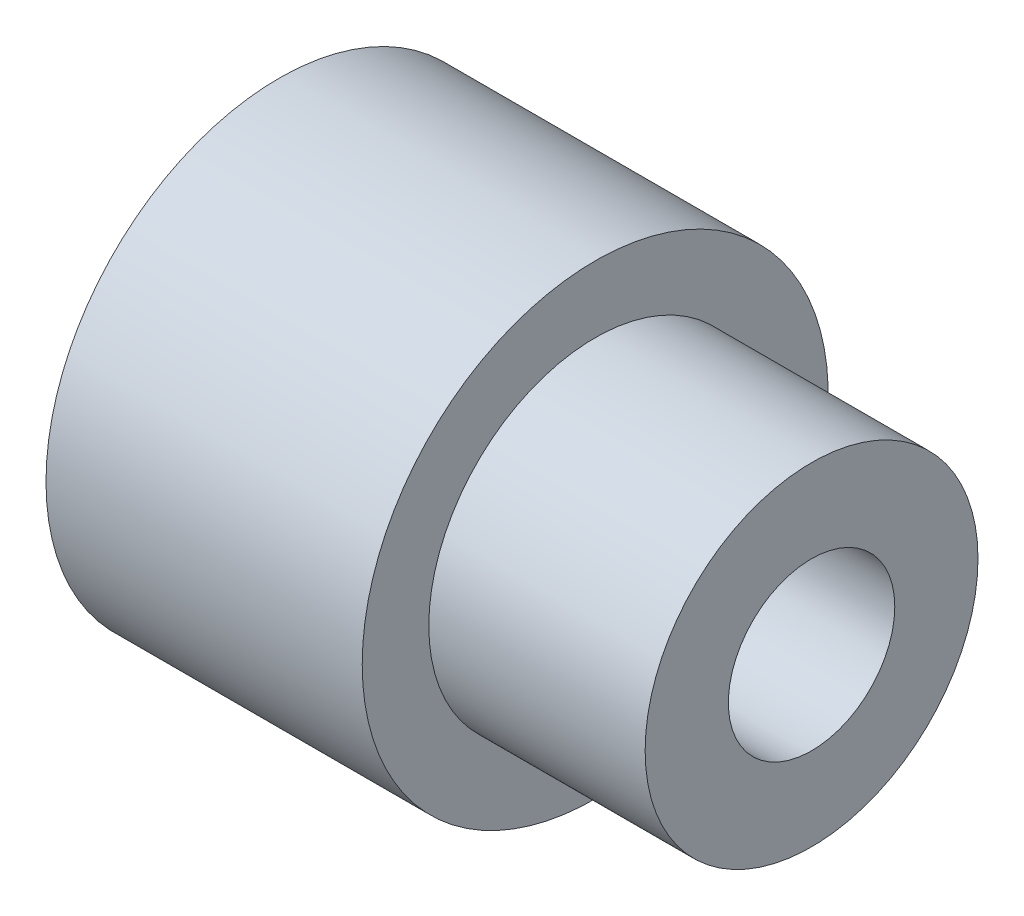
SolidWorks part; units mm, degrees
ref_plane "Front Plane" through (0, 0, 0) normal (0, 0, 1) x (1, 0, 0)
ref_plane "Top Plane" through (0, 0, 0) normal (0, 1, 0) x (1, 0, 0)
ref_plane "Right Plane" through (0, 0, 0) normal (1, 0, 0) x (0, 0, -1)
sketch "Sketch1" plane through (0, 0, 0) normal (0, 0, 1) x (1, 0, 0)
  line L0 (-20.8099, 0) -> (11.1901, 0) construction
  line L1 (-20.8099, 0) -> (-20.8099, -14)
  line L2 (-20.8099, -14) -> (-1.8099, -14)
  line L3 (-1.8099, -14) -> (-1.8099, -10)
  line L4 (-1.8099, -10) -> (11.1901, -10)
  line L5 (11.1901, -10) -> (11.1901, 0)
  line L6 (-20.8099, 0) -> (11.1901, 0)
  dimension "D1" = 14
  dimension "D2" = 19
  dimension "D3" = 13
  dimension "D4" = 4
  dimension "D5" = 10
  dimension "D6" = 32
revolve "Revolve1" add sketch "Sketch1" angle 360 about L0
sketch "Sketch2" plane through (-20.8099, 0, 0) normal (-1, 0, 0) x (0, 0, 1)
  circle A0 centre (0, 0) radius 11
  dimension "D1" = 22
extrude "Cut-Extrude2" cut sketch "Sketch2" against normal blind 6
sketch "Sketch6" plane through (-14.8099, 0, 0) normal (-1, 0, 0) x (0, 0, 1)
  circle A0 centre (0, 0) radius 9
  dimension "D1" = 18
extrude "Cut-Extrude3" cut sketch "Sketch6" against normal blind 10
sketch "Sketch7" plane through (11.1901, 0, 0) normal (1, 0, 0) x (0, 0, -1)
  circle A0 centre (0, 0) radius 5
  dimension "D1" = 10
extrude "Cut-Extrude4" cut sketch "Sketch7" against normal through all and the other way through all
